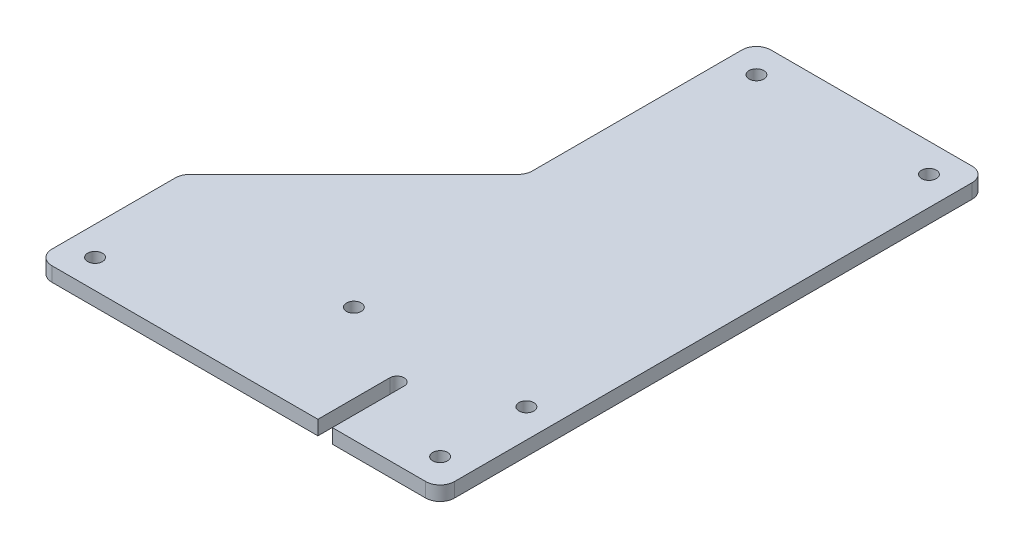
SolidWorks part; units mm, degrees
ref_plane "Front Plane" through (0, 0, 0) normal (0, 0, 1) x (1, 0, 0)
ref_plane "Top Plane" through (0, 0, 0) normal (0, 1, 0) x (1, 0, 0)
ref_plane "Right Plane" through (0, 0, 0) normal (1, 0, 0) x (0, 0, -1)
sketch "Sketch1" plane through (0, 0, 0) normal (0, 1, 0) x (1, 0, 0)
  line L0 (-76.2, 0) -> (76.2, 0) construction
  line L1 (0, 38.1) -> (76.2, 38.1) construction
  line L2 (0, 215.9) -> (76.2, 215.9) construction
  line L3 (-12.7, 228.6) -> (88.9, 228.6)
  line L4 (88.9, 228.6) -> (88.9, -12.7)
  line L5 (88.9, -12.7) -> (-88.9, -12.7)
  line L6 (-88.9, -12.7) -> (-88.9, 50.8)
  line L7 (-88.9, 50.8) -> (-12.7, 127)
  line L8 (-12.7, 127) -> (-12.7, 228.6)
  point P0 (-76.2, 0)
  point P1 (76.2, 0)
  dimension "D1" = 152.4
  dimension "D2" = 76.2
  dimension "D3" = 38.1
  dimension "D4" = 177.8
  dimension "D5" = 12.7
  dimension "D6" = 101.6
  dimension "D7" = 12.7
  dimension "D8" = 177.8
  dimension "D9" = 12.7
  dimension "D10" = 45
  dimension "D11" = 12.7
extrude "Boss-Extrude1" add sketch "Sketch1" along normal blind 6.35
hole_wizard "1/4 Clearance Hole1" positions "Sketch3" profile "Sketch2" hole size "1/4" standard "ANSI Inch"
sketch "Sketch3" plane through (0, 6.35, 0) normal (0, 1, 0) x (1, 0, 0)
  point P0 (76.2, 215.9)
  point P2 (0, 215.9)
  point P9 (0, 38.1)
  point P12 (76.2, 38.1)
  point P15 (76.2, 0)
  point P18 (-76.2, 0)
sketch "Sketch2" plane through (76.2, 6.35, -215.9) normal (1, 0, 0) x (0, 0, 1)
  line L0 (0, 0) -> (0, 8.3111)
  line L1 (0, 8.3111) -> (3.2639, 6.35)
  line L2 (3.2639, 6.35) -> (3.2639, 0)
  line L5 (3.2639, 0) -> (0, 0)
  line L10 (0, 8.3111) -> (-3.2639, 6.35) construction
  line L11 (0, -6.35) -> (0, 107.95) construction
  dimension "Hole Dia." = 6.5278
  dimension "Hole Depth" = 6.35
  dimension "Drill Angle" = 118
fillet "Fillet1" radius 6.35 6 edges at (-12.7, 3.175, -228.6) (88.9, 3.175, -228.6) (88.9, 3.175, 12.7) (-88.9, 3.175, 12.7) (-88.9, 3.175, -50.8) (-12.7, 3.175, -127)
sketch "Sketch4" plane through (0, 6.35, 0) normal (0, 1, 0) x (1, 0, 0)
  line L0 (0, 38.1) -> (76.2, 38.1) construction
  line L1 (38.1, 19.05) -> (38.1, -12.7) construction
  line L2 (-82.55, -12.7) -> (82.55, -12.7) construction
  line L3 (41.275, 19.05) -> (41.275, -12.7)
  line L4 (34.925, 19.05) -> (34.925, -12.7)
  arc A0 (41.275, 19.05) -> (34.925, 19.05) centre (38.1, 19.05) ccw
  arc A1 (34.925, -12.7) -> (41.275, -12.7) centre (38.1, -12.7) ccw
  point P8 (38.1, 3.175)
  point P13 (38.1, 38.1)
  dimension "D1" = 6.35
  dimension "D2" = 31.75
extrude "Cut-Extrude1" cut sketch "Sketch4" against normal up to next
